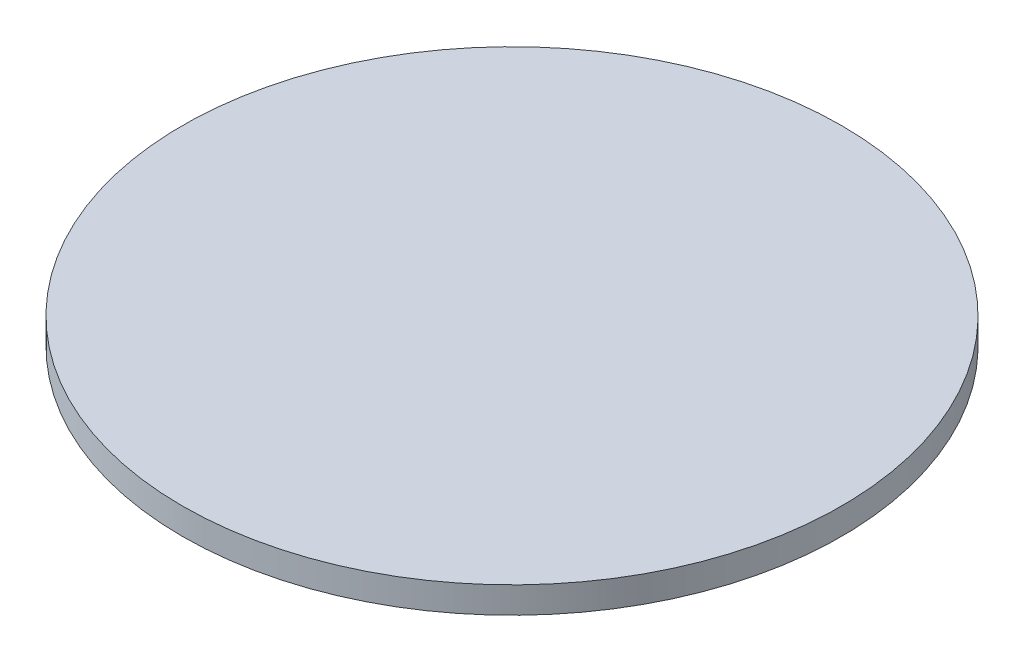
SolidWorks part; units mm, degrees
ref_plane "前视基准面" through (0, 0, 0) normal (0, 0, 1) x (1, 0, 0)
ref_plane "上视基准面" through (0, 0, 0) normal (0, 1, 0) x (1, 0, 0)
ref_plane "右视基准面" through (0, 0, 0) normal (1, 0, 0) x (0, 0, -1)
sketch "草图1" plane through (0, 0, 0) normal (0, 1, 0) x (1, 0, 0)
  circle A0 centre (0, 0) radius 25
  dimension "D1" = 50
extrude "凸台-拉伸1" add sketch "草图1" along normal blind 2
